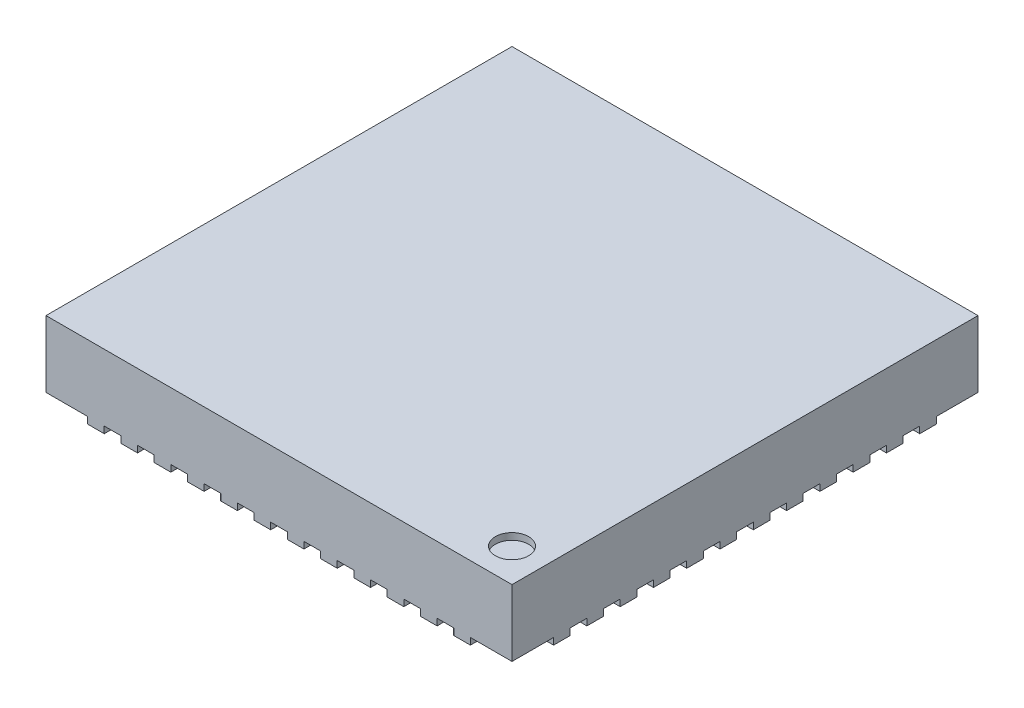
SolidWorks part; units mm, degrees
ref_plane "Front Plane" through (0, 0, 0) normal (0, 0, 1) x (1, 0, 0)
ref_plane "Top Plane" through (0, 0, 0) normal (0, 1, 0) x (1, 0, 0)
ref_plane "Right Plane" through (0, 0, 0) normal (1, 0, 0) x (0, 0, -1)
ref_plane "Plane1" through (0, 0, 0) normal (0, -1, 0) x (1, 0, 0)
sketch "Sketch1" plane through (0, 0, 0) normal (0, -1, 0) x (1, 0, 0)
  line L0 (3.5, 3.5) -> (-3.5, 3.5)
  line L1 (-3.5, 3.5) -> (-3.5, -3.5)
  line L2 (-3.5, -3.5) -> (3.5, -3.5)
  line L3 (3.5, -3.5) -> (3.5, 3.5)
extrude "Boss-Extrude1" add sketch "Sketch1" against normal blind 1
sketch "Sketch2" plane through (0, 0, 0) normal (0, -1, 0) x (1, 0, 0)
  line L0 (-3.5, 2.875) -> (-3.225, 2.875)
  line L1 (-3.225, 2.625) -> (-3.5, 2.625)
  line L2 (-3.5, 2.625) -> (-3.5, 2.875)
  arc A0 (-3.225, 2.875) -> (-3.225, 2.625) centre (-3.225, 2.75) cw
extrude "Boss-Extrude2" add sketch "Sketch2" along normal blind 0.1
sketch "Sketch3" plane through (0, 0, 0) normal (0, -1, 0) x (1, 0, 0)
  line L0 (-3.5, 2.375) -> (-3.225, 2.375)
  line L1 (-3.225, 2.125) -> (-3.5, 2.125)
  line L2 (-3.5, 2.125) -> (-3.5, 2.375)
  arc A0 (-3.225, 2.375) -> (-3.225, 2.125) centre (-3.225, 2.25) cw
extrude "Boss-Extrude3" add sketch "Sketch3" along normal blind 0.1
sketch "Sketch4" plane through (0, 0, 0) normal (0, -1, 0) x (1, 0, 0)
  line L0 (-3.5, 1.875) -> (-3.225, 1.875)
  line L1 (-3.225, 1.625) -> (-3.5, 1.625)
  line L2 (-3.5, 1.625) -> (-3.5, 1.875)
  arc A0 (-3.225, 1.875) -> (-3.225, 1.625) centre (-3.225, 1.75) cw
extrude "Boss-Extrude4" add sketch "Sketch4" along normal blind 0.1
sketch "Sketch5" plane through (0, 0, 0) normal (0, -1, 0) x (1, 0, 0)
  line L0 (-3.5, 1.375) -> (-3.225, 1.375)
  line L1 (-3.225, 1.125) -> (-3.5, 1.125)
  line L2 (-3.5, 1.125) -> (-3.5, 1.375)
  arc A0 (-3.225, 1.375) -> (-3.225, 1.125) centre (-3.225, 1.25) cw
extrude "Boss-Extrude5" add sketch "Sketch5" along normal blind 0.1
sketch "Sketch6" plane through (0, 0, 0) normal (0, -1, 0) x (1, 0, 0)
  line L0 (-3.5, 0.875) -> (-3.225, 0.875)
  line L1 (-3.225, 0.625) -> (-3.5, 0.625)
  line L2 (-3.5, 0.625) -> (-3.5, 0.875)
  arc A0 (-3.225, 0.875) -> (-3.225, 0.625) centre (-3.225, 0.75) cw
extrude "Boss-Extrude6" add sketch "Sketch6" along normal blind 0.1
sketch "Sketch7" plane through (0, 0, 0) normal (0, -1, 0) x (1, 0, 0)
  line L0 (-3.5, 0.375) -> (-3.225, 0.375)
  line L1 (-3.225, 0.125) -> (-3.5, 0.125)
  line L2 (-3.5, 0.125) -> (-3.5, 0.375)
  arc A0 (-3.225, 0.375) -> (-3.225, 0.125) centre (-3.225, 0.25) cw
extrude "Boss-Extrude7" add sketch "Sketch7" along normal blind 0.1
sketch "Sketch8" plane through (0, 0, 0) normal (0, -1, 0) x (1, 0, 0)
  line L0 (-3.5, -0.125) -> (-3.225, -0.125)
  line L1 (-3.225, -0.375) -> (-3.5, -0.375)
  line L2 (-3.5, -0.375) -> (-3.5, -0.125)
  arc A0 (-3.225, -0.125) -> (-3.225, -0.375) centre (-3.225, -0.25) cw
extrude "Boss-Extrude8" add sketch "Sketch8" along normal blind 0.1
sketch "Sketch9" plane through (0, 0, 0) normal (0, -1, 0) x (1, 0, 0)
  line L0 (-3.5, -0.625) -> (-3.225, -0.625)
  line L1 (-3.225, -0.875) -> (-3.5, -0.875)
  line L2 (-3.5, -0.875) -> (-3.5, -0.625)
  arc A0 (-3.225, -0.625) -> (-3.225, -0.875) centre (-3.225, -0.75) cw
extrude "Boss-Extrude9" add sketch "Sketch9" along normal blind 0.1
sketch "Sketch10" plane through (0, 0, 0) normal (0, -1, 0) x (1, 0, 0)
  line L0 (-3.5, -1.125) -> (-3.225, -1.125)
  line L1 (-3.225, -1.375) -> (-3.5, -1.375)
  line L2 (-3.5, -1.375) -> (-3.5, -1.125)
  arc A0 (-3.225, -1.125) -> (-3.225, -1.375) centre (-3.225, -1.25) cw
extrude "Boss-Extrude10" add sketch "Sketch10" along normal blind 0.1
sketch "Sketch11" plane through (0, 0, 0) normal (0, -1, 0) x (1, 0, 0)
  line L0 (-3.5, -1.625) -> (-3.225, -1.625)
  line L1 (-3.225, -1.875) -> (-3.5, -1.875)
  line L2 (-3.5, -1.875) -> (-3.5, -1.625)
  arc A0 (-3.225, -1.625) -> (-3.225, -1.875) centre (-3.225, -1.75) cw
extrude "Boss-Extrude11" add sketch "Sketch11" along normal blind 0.1
sketch "Sketch12" plane through (0, 0, 0) normal (0, -1, 0) x (1, 0, 0)
  line L0 (-3.5, -2.125) -> (-3.225, -2.125)
  line L1 (-3.225, -2.375) -> (-3.5, -2.375)
  line L2 (-3.5, -2.375) -> (-3.5, -2.125)
  arc A0 (-3.225, -2.125) -> (-3.225, -2.375) centre (-3.225, -2.25) cw
extrude "Boss-Extrude12" add sketch "Sketch12" along normal blind 0.1
sketch "Sketch13" plane through (0, 0, 0) normal (0, -1, 0) x (1, 0, 0)
  line L0 (-3.5, -2.625) -> (-3.225, -2.625)
  line L1 (-3.225, -2.875) -> (-3.5, -2.875)
  line L2 (-3.5, -2.875) -> (-3.5, -2.625)
  arc A0 (-3.225, -2.625) -> (-3.225, -2.875) centre (-3.225, -2.75) cw
extrude "Boss-Extrude13" add sketch "Sketch13" along normal blind 0.1
sketch "Sketch14" plane through (0, 0, 0) normal (0, -1, 0) x (1, 0, 0)
  line L0 (-2.875, -3.5) -> (-2.875, -3.225)
  line L1 (-2.625, -3.225) -> (-2.625, -3.5)
  line L2 (-2.625, -3.5) -> (-2.875, -3.5)
  arc A0 (-2.875, -3.225) -> (-2.625, -3.225) centre (-2.75, -3.225) cw
extrude "Boss-Extrude14" add sketch "Sketch14" along normal blind 0.1
sketch "Sketch15" plane through (0, 0, 0) normal (0, -1, 0) x (1, 0, 0)
  line L0 (-2.375, -3.5) -> (-2.375, -3.225)
  line L1 (-2.125, -3.225) -> (-2.125, -3.5)
  line L2 (-2.125, -3.5) -> (-2.375, -3.5)
  arc A0 (-2.375, -3.225) -> (-2.125, -3.225) centre (-2.25, -3.225) cw
extrude "Boss-Extrude15" add sketch "Sketch15" along normal blind 0.1
sketch "Sketch16" plane through (0, 0, 0) normal (0, -1, 0) x (1, 0, 0)
  line L0 (-1.875, -3.5) -> (-1.875, -3.225)
  line L1 (-1.625, -3.225) -> (-1.625, -3.5)
  line L2 (-1.625, -3.5) -> (-1.875, -3.5)
  arc A0 (-1.875, -3.225) -> (-1.625, -3.225) centre (-1.75, -3.225) cw
extrude "Boss-Extrude16" add sketch "Sketch16" along normal blind 0.1
sketch "Sketch17" plane through (0, 0, 0) normal (0, -1, 0) x (1, 0, 0)
  line L0 (-1.375, -3.5) -> (-1.375, -3.225)
  line L1 (-1.125, -3.225) -> (-1.125, -3.5)
  line L2 (-1.125, -3.5) -> (-1.375, -3.5)
  arc A0 (-1.375, -3.225) -> (-1.125, -3.225) centre (-1.25, -3.225) cw
extrude "Boss-Extrude17" add sketch "Sketch17" along normal blind 0.1
sketch "Sketch18" plane through (0, 0, 0) normal (0, -1, 0) x (1, 0, 0)
  line L0 (-0.875, -3.5) -> (-0.875, -3.225)
  line L1 (-0.625, -3.225) -> (-0.625, -3.5)
  line L2 (-0.625, -3.5) -> (-0.875, -3.5)
  arc A0 (-0.875, -3.225) -> (-0.625, -3.225) centre (-0.75, -3.225) cw
extrude "Boss-Extrude18" add sketch "Sketch18" along normal blind 0.1
sketch "Sketch19" plane through (0, 0, 0) normal (0, -1, 0) x (1, 0, 0)
  line L0 (-0.375, -3.5) -> (-0.375, -3.225)
  line L1 (-0.125, -3.225) -> (-0.125, -3.5)
  line L2 (-0.125, -3.5) -> (-0.375, -3.5)
  arc A0 (-0.375, -3.225) -> (-0.125, -3.225) centre (-0.25, -3.225) cw
extrude "Boss-Extrude19" add sketch "Sketch19" along normal blind 0.1
sketch "Sketch20" plane through (0, 0, 0) normal (0, -1, 0) x (1, 0, 0)
  line L0 (0.125, -3.5) -> (0.125, -3.225)
  line L1 (0.375, -3.225) -> (0.375, -3.5)
  line L2 (0.375, -3.5) -> (0.125, -3.5)
  arc A0 (0.125, -3.225) -> (0.375, -3.225) centre (0.25, -3.225) cw
extrude "Boss-Extrude20" add sketch "Sketch20" along normal blind 0.1
sketch "Sketch21" plane through (0, 0, 0) normal (0, -1, 0) x (1, 0, 0)
  line L0 (0.625, -3.5) -> (0.625, -3.225)
  line L1 (0.875, -3.225) -> (0.875, -3.5)
  line L2 (0.875, -3.5) -> (0.625, -3.5)
  arc A0 (0.625, -3.225) -> (0.875, -3.225) centre (0.75, -3.225) cw
extrude "Boss-Extrude21" add sketch "Sketch21" along normal blind 0.1
sketch "Sketch22" plane through (0, 0, 0) normal (0, -1, 0) x (1, 0, 0)
  line L0 (1.125, -3.5) -> (1.125, -3.225)
  line L1 (1.375, -3.225) -> (1.375, -3.5)
  line L2 (1.375, -3.5) -> (1.125, -3.5)
  arc A0 (1.125, -3.225) -> (1.375, -3.225) centre (1.25, -3.225) cw
extrude "Boss-Extrude22" add sketch "Sketch22" along normal blind 0.1
sketch "Sketch23" plane through (0, 0, 0) normal (0, -1, 0) x (1, 0, 0)
  line L0 (1.625, -3.5) -> (1.625, -3.225)
  line L1 (1.875, -3.225) -> (1.875, -3.5)
  line L2 (1.875, -3.5) -> (1.625, -3.5)
  arc A0 (1.625, -3.225) -> (1.875, -3.225) centre (1.75, -3.225) cw
extrude "Boss-Extrude23" add sketch "Sketch23" along normal blind 0.1
sketch "Sketch24" plane through (0, 0, 0) normal (0, -1, 0) x (1, 0, 0)
  line L0 (2.125, -3.5) -> (2.125, -3.225)
  line L1 (2.375, -3.225) -> (2.375, -3.5)
  line L2 (2.375, -3.5) -> (2.125, -3.5)
  arc A0 (2.125, -3.225) -> (2.375, -3.225) centre (2.25, -3.225) cw
extrude "Boss-Extrude24" add sketch "Sketch24" along normal blind 0.1
sketch "Sketch25" plane through (0, 0, 0) normal (0, -1, 0) x (1, 0, 0)
  line L0 (2.625, -3.5) -> (2.625, -3.225)
  line L1 (2.875, -3.225) -> (2.875, -3.5)
  line L2 (2.875, -3.5) -> (2.625, -3.5)
  arc A0 (2.625, -3.225) -> (2.875, -3.225) centre (2.75, -3.225) cw
extrude "Boss-Extrude25" add sketch "Sketch25" along normal blind 0.1
sketch "Sketch26" plane through (0, 0, 0) normal (0, -1, 0) x (1, 0, 0)
  line L0 (3.5, -2.875) -> (3.225, -2.875)
  line L1 (3.225, -2.625) -> (3.5, -2.625)
  line L2 (3.5, -2.625) -> (3.5, -2.875)
  arc A0 (3.225, -2.875) -> (3.225, -2.625) centre (3.225, -2.75) cw
extrude "Boss-Extrude26" add sketch "Sketch26" along normal blind 0.1
sketch "Sketch27" plane through (0, 0, 0) normal (0, -1, 0) x (1, 0, 0)
  line L0 (3.5, -2.375) -> (3.225, -2.375)
  line L1 (3.225, -2.125) -> (3.5, -2.125)
  line L2 (3.5, -2.125) -> (3.5, -2.375)
  arc A0 (3.225, -2.375) -> (3.225, -2.125) centre (3.225, -2.25) cw
extrude "Boss-Extrude27" add sketch "Sketch27" along normal blind 0.1
sketch "Sketch28" plane through (0, 0, 0) normal (0, -1, 0) x (1, 0, 0)
  line L0 (3.5, -1.875) -> (3.225, -1.875)
  line L1 (3.225, -1.625) -> (3.5, -1.625)
  line L2 (3.5, -1.625) -> (3.5, -1.875)
  arc A0 (3.225, -1.875) -> (3.225, -1.625) centre (3.225, -1.75) cw
extrude "Boss-Extrude28" add sketch "Sketch28" along normal blind 0.1
sketch "Sketch29" plane through (0, 0, 0) normal (0, -1, 0) x (1, 0, 0)
  line L0 (3.5, -1.375) -> (3.225, -1.375)
  line L1 (3.225, -1.125) -> (3.5, -1.125)
  line L2 (3.5, -1.125) -> (3.5, -1.375)
  arc A0 (3.225, -1.375) -> (3.225, -1.125) centre (3.225, -1.25) cw
extrude "Boss-Extrude29" add sketch "Sketch29" along normal blind 0.1
sketch "Sketch30" plane through (0, 0, 0) normal (0, -1, 0) x (1, 0, 0)
  line L0 (3.5, -0.875) -> (3.225, -0.875)
  line L1 (3.225, -0.625) -> (3.5, -0.625)
  line L2 (3.5, -0.625) -> (3.5, -0.875)
  arc A0 (3.225, -0.875) -> (3.225, -0.625) centre (3.225, -0.75) cw
extrude "Boss-Extrude30" add sketch "Sketch30" along normal blind 0.1
sketch "Sketch31" plane through (0, 0, 0) normal (0, -1, 0) x (1, 0, 0)
  line L0 (3.5, -0.375) -> (3.225, -0.375)
  line L1 (3.225, -0.125) -> (3.5, -0.125)
  line L2 (3.5, -0.125) -> (3.5, -0.375)
  arc A0 (3.225, -0.375) -> (3.225, -0.125) centre (3.225, -0.25) cw
extrude "Boss-Extrude31" add sketch "Sketch31" along normal blind 0.1
sketch "Sketch32" plane through (0, 0, 0) normal (0, -1, 0) x (1, 0, 0)
  line L0 (3.5, 0.125) -> (3.225, 0.125)
  line L1 (3.225, 0.375) -> (3.5, 0.375)
  line L2 (3.5, 0.375) -> (3.5, 0.125)
  arc A0 (3.225, 0.125) -> (3.225, 0.375) centre (3.225, 0.25) cw
extrude "Boss-Extrude32" add sketch "Sketch32" along normal blind 0.1
sketch "Sketch33" plane through (0, 0, 0) normal (0, -1, 0) x (1, 0, 0)
  line L0 (3.5, 0.625) -> (3.225, 0.625)
  line L1 (3.225, 0.875) -> (3.5, 0.875)
  line L2 (3.5, 0.875) -> (3.5, 0.625)
  arc A0 (3.225, 0.625) -> (3.225, 0.875) centre (3.225, 0.75) cw
extrude "Boss-Extrude33" add sketch "Sketch33" along normal blind 0.1
sketch "Sketch34" plane through (0, 0, 0) normal (0, -1, 0) x (1, 0, 0)
  line L0 (3.5, 1.125) -> (3.225, 1.125)
  line L1 (3.225, 1.375) -> (3.5, 1.375)
  line L2 (3.5, 1.375) -> (3.5, 1.125)
  arc A0 (3.225, 1.125) -> (3.225, 1.375) centre (3.225, 1.25) cw
extrude "Boss-Extrude34" add sketch "Sketch34" along normal blind 0.1
sketch "Sketch35" plane through (0, 0, 0) normal (0, -1, 0) x (1, 0, 0)
  line L0 (3.5, 1.625) -> (3.225, 1.625)
  line L1 (3.225, 1.875) -> (3.5, 1.875)
  line L2 (3.5, 1.875) -> (3.5, 1.625)
  arc A0 (3.225, 1.625) -> (3.225, 1.875) centre (3.225, 1.75) cw
extrude "Boss-Extrude35" add sketch "Sketch35" along normal blind 0.1
sketch "Sketch36" plane through (0, 0, 0) normal (0, -1, 0) x (1, 0, 0)
  line L0 (3.5, 2.125) -> (3.225, 2.125)
  line L1 (3.225, 2.375) -> (3.5, 2.375)
  line L2 (3.5, 2.375) -> (3.5, 2.125)
  arc A0 (3.225, 2.125) -> (3.225, 2.375) centre (3.225, 2.25) cw
extrude "Boss-Extrude36" add sketch "Sketch36" along normal blind 0.1
sketch "Sketch37" plane through (0, 0, 0) normal (0, -1, 0) x (1, 0, 0)
  line L0 (3.5, 2.625) -> (3.225, 2.625)
  line L1 (3.225, 2.875) -> (3.5, 2.875)
  line L2 (3.5, 2.875) -> (3.5, 2.625)
  arc A0 (3.225, 2.625) -> (3.225, 2.875) centre (3.225, 2.75) cw
extrude "Boss-Extrude37" add sketch "Sketch37" along normal blind 0.1
sketch "Sketch38" plane through (0, 0, 0) normal (0, -1, 0) x (1, 0, 0)
  line L0 (2.375, 3.5) -> (2.375, 3.225)
  line L1 (2.125, 3.225) -> (2.125, 3.5)
  line L2 (2.125, 3.5) -> (2.375, 3.5)
  arc A0 (2.375, 3.225) -> (2.125, 3.225) centre (2.25, 3.225) cw
extrude "Boss-Extrude38" add sketch "Sketch38" along normal blind 0.1
sketch "Sketch39" plane through (0, 0, 0) normal (0, -1, 0) x (1, 0, 0)
  line L0 (1.875, 3.5) -> (1.875, 3.225)
  line L1 (1.625, 3.225) -> (1.625, 3.5)
  line L2 (1.625, 3.5) -> (1.875, 3.5)
  arc A0 (1.875, 3.225) -> (1.625, 3.225) centre (1.75, 3.225) cw
extrude "Boss-Extrude39" add sketch "Sketch39" along normal blind 0.1
sketch "Sketch40" plane through (0, 0, 0) normal (0, -1, 0) x (1, 0, 0)
  line L0 (1.375, 3.5) -> (1.375, 3.225)
  line L1 (1.125, 3.225) -> (1.125, 3.5)
  line L2 (1.125, 3.5) -> (1.375, 3.5)
  arc A0 (1.375, 3.225) -> (1.125, 3.225) centre (1.25, 3.225) cw
extrude "Boss-Extrude40" add sketch "Sketch40" along normal blind 0.1
sketch "Sketch41" plane through (0, 0, 0) normal (0, -1, 0) x (1, 0, 0)
  line L0 (0.875, 3.5) -> (0.875, 3.225)
  line L1 (0.625, 3.225) -> (0.625, 3.5)
  line L2 (0.625, 3.5) -> (0.875, 3.5)
  arc A0 (0.875, 3.225) -> (0.625, 3.225) centre (0.75, 3.225) cw
extrude "Boss-Extrude41" add sketch "Sketch41" along normal blind 0.1
sketch "Sketch42" plane through (0, 0, 0) normal (0, -1, 0) x (1, 0, 0)
  line L0 (0.375, 3.5) -> (0.375, 3.225)
  line L1 (0.125, 3.225) -> (0.125, 3.5)
  line L2 (0.125, 3.5) -> (0.375, 3.5)
  arc A0 (0.375, 3.225) -> (0.125, 3.225) centre (0.25, 3.225) cw
extrude "Boss-Extrude42" add sketch "Sketch42" along normal blind 0.1
sketch "Sketch43" plane through (0, 0, 0) normal (0, -1, 0) x (1, 0, 0)
  line L0 (-0.125, 3.5) -> (-0.125, 3.225)
  line L1 (-0.375, 3.225) -> (-0.375, 3.5)
  line L2 (-0.375, 3.5) -> (-0.125, 3.5)
  arc A0 (-0.125, 3.225) -> (-0.375, 3.225) centre (-0.25, 3.225) cw
extrude "Boss-Extrude43" add sketch "Sketch43" along normal blind 0.1
sketch "Sketch44" plane through (0, 0, 0) normal (0, -1, 0) x (1, 0, 0)
  line L0 (-0.625, 3.5) -> (-0.625, 3.225)
  line L1 (-0.875, 3.225) -> (-0.875, 3.5)
  line L2 (-0.875, 3.5) -> (-0.625, 3.5)
  arc A0 (-0.625, 3.225) -> (-0.875, 3.225) centre (-0.75, 3.225) cw
extrude "Boss-Extrude44" add sketch "Sketch44" along normal blind 0.1
sketch "Sketch45" plane through (0, 0, 0) normal (0, -1, 0) x (1, 0, 0)
  line L0 (-1.125, 3.5) -> (-1.125, 3.225)
  line L1 (-1.375, 3.225) -> (-1.375, 3.5)
  line L2 (-1.375, 3.5) -> (-1.125, 3.5)
  arc A0 (-1.125, 3.225) -> (-1.375, 3.225) centre (-1.25, 3.225) cw
extrude "Boss-Extrude45" add sketch "Sketch45" along normal blind 0.1
sketch "Sketch46" plane through (0, 0, 0) normal (0, -1, 0) x (1, 0, 0)
  line L0 (-1.625, 3.5) -> (-1.625, 3.225)
  line L1 (-1.875, 3.225) -> (-1.875, 3.5)
  line L2 (-1.875, 3.5) -> (-1.625, 3.5)
  arc A0 (-1.625, 3.225) -> (-1.875, 3.225) centre (-1.75, 3.225) cw
extrude "Boss-Extrude46" add sketch "Sketch46" along normal blind 0.1
sketch "Sketch47" plane through (0, 0, 0) normal (0, -1, 0) x (1, 0, 0)
  line L0 (-2.125, 3.5) -> (-2.125, 3.225)
  line L1 (-2.375, 3.225) -> (-2.375, 3.5)
  line L2 (-2.375, 3.5) -> (-2.125, 3.5)
  arc A0 (-2.125, 3.225) -> (-2.375, 3.225) centre (-2.25, 3.225) cw
extrude "Boss-Extrude47" add sketch "Sketch47" along normal blind 0.1
sketch "Sketch48" plane through (0, 0, 0) normal (0, -1, 0) x (1, 0, 0)
  line L0 (-2.625, 3.5) -> (-2.625, 3.225)
  line L1 (-2.875, 3.225) -> (-2.875, 3.5)
  line L2 (-2.875, 3.5) -> (-2.625, 3.5)
  arc A0 (-2.625, 3.225) -> (-2.875, 3.225) centre (-2.75, 3.225) cw
extrude "Boss-Extrude48" add sketch "Sketch48" along normal blind 0.1
sketch "Sketch49" plane through (0, 0, 0) normal (0, -1, 0) x (1, 0, 0)
  line L0 (2.875, 3.5) -> (2.875, 3.225)
  line L1 (2.625, 3.225) -> (2.625, 3.5)
  line L2 (2.625, 3.5) -> (2.875, 3.5)
  arc A0 (2.875, 3.225) -> (2.625, 3.225) centre (2.75, 3.225) cw
extrude "Boss-Extrude49" add sketch "Sketch49" along normal blind 0.1
sketch "Sketch50" plane through (0, 0, 0) normal (0, -1, 0) x (1, 0, 0)
  line L0 (2.5, -2.75) -> (-2.5, -2.75)
  line L1 (-2.75, -2.5) -> (-2.75, 2.5)
  line L2 (-2.5, 2.75) -> (2.5, 2.75)
  line L3 (2.5, 2.75) -> (2.75, 2.5)
  line L4 (2.75, 2.5) -> (2.75, -2.5)
  arc A0 (2.75, -2.5) -> (2.5, -2.75) centre (2.5, -2.5) cw
  arc A1 (-2.5, -2.75) -> (-2.75, -2.5) centre (-2.5, -2.5) cw
  arc A2 (-2.75, 2.5) -> (-2.5, 2.75) centre (-2.5, 2.5) cw
extrude "Boss-Extrude50" add sketch "Sketch50" along normal blind 0.1
ref_plane "Plane2" through (0, 0, 3) normal (0, 0, -1) x (-1, 0, 0)
sketch "Sketch51" plane through (0, 0, 3) normal (0, 0, -1) x (-1, 0, 0)
  line L0 (-3.25, 0.9) -> (-3, 0.9)
  line L1 (-3, 0.9) -> (-3, 1)
  line L2 (-3, 1) -> (-3.25, 1)
  line L3 (-3.25, 1) -> (-3.25, 0.9)
  line L4 (-3, 0.9) -> (-3, 1) construction
revolve "Cut-Revolve1" cut sketch "Sketch51" angle 360 about L4
